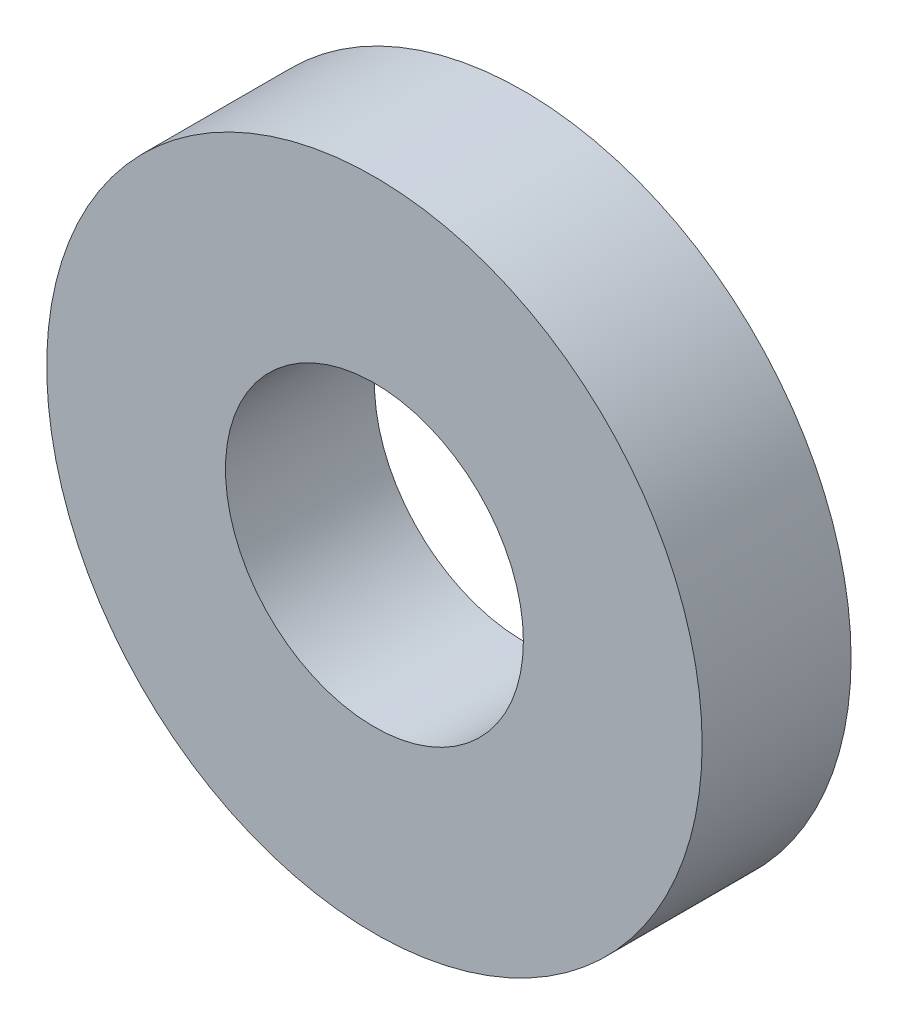
SolidWorks part; units mm, degrees
ref_plane "Front Plane" through (0, 0, 0) normal (0, 0, 1) x (1, 0, 0)
ref_plane "Top Plane" through (0, 0, 0) normal (0, 1, 0) x (1, 0, 0)
ref_plane "Right Plane" through (0, 0, 0) normal (1, 0, 0) x (0, 0, -1)
sketch "Sketch1" plane through (0, 0, 0) normal (0, 0, 1) x (1, 0, 0)
  circle A0 centre (0, 0) radius 6
  circle A1 centre (0, 0) radius 13.2
extrude "Boss-Extrude1" add sketch "Sketch1" along normal blind 6
sketch "Sketch2" plane through (0, 0, 6) normal (0, 0, 1) x (1, 0, 0)
  line L0 (0, 0) -> (0, 15.2) construction
  line L1 (-1.8199, 15.2) -> (0, 0) construction
  line L2 (1.8199, 15.2) -> (0, 0) construction
  arc A0 (-1.8199, 12) -> (1.8199, 12) centre (0, 0) cw
  arc A1 (-6.8199, 11.3018) -> (0.0279, 13.2) centre (0, 0) ccw
  arc A2 (-1.8199, 10.512) -> (1.8199, 10.512) centre (0, 0) cw
  arc A3 (-6.8199, 11.3018) -> (-1.8199, 12) centre (-4.3199, 11.6509) ccw
  arc A4 (0.0279, 13.2) -> (1.8199, 12) centre (0.0238, 11.2558) ccw
